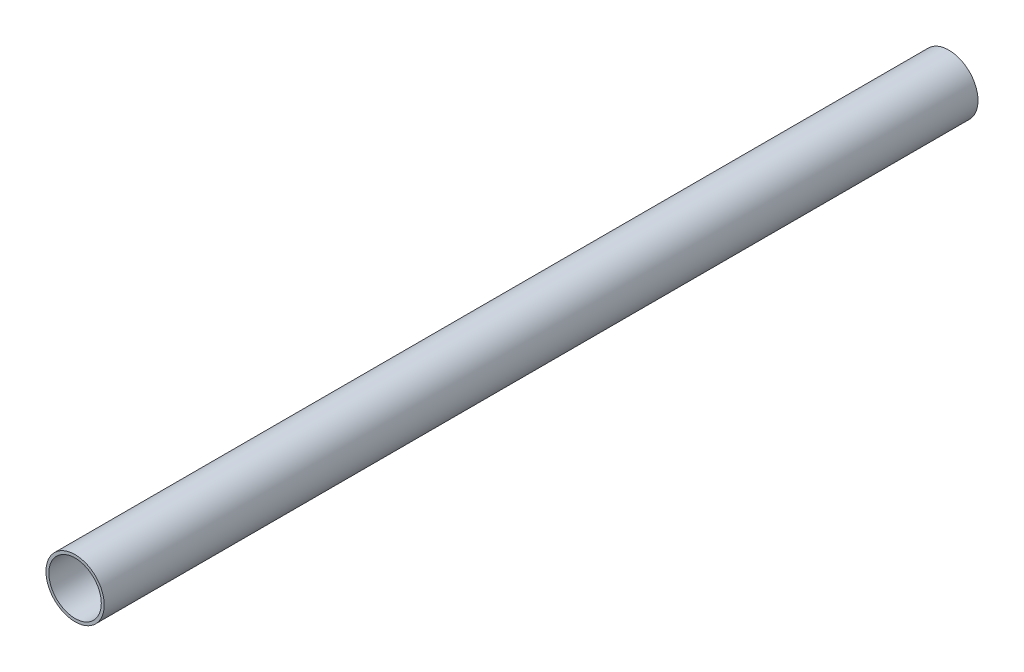
SolidWorks part; units mm, degrees
material "Thornel Mat VMA"
ref_plane "Plan de face" through (0, 0, 0) normal (0, 0, 1) x (1, 0, 0)
ref_plane "Plan de dessus" through (0, 0, 0) normal (0, 1, 0) x (1, 0, 0)
ref_plane "Plan de droite" through (0, 0, 0) normal (1, 0, 0) x (0, 0, -1)
sketch "Esquisse1" plane through (0, 0, 0) normal (0, 0, 1) x (1, 0, 0)
  circle A0 centre (0, 0) radius 5
  circle A1 centre (0, 0) radius 4.5
  dimension "D1" = 9
  dimension "D2" = 10
extrude "Boss.-Extru.1" add sketch "Esquisse1" along normal blind 150
